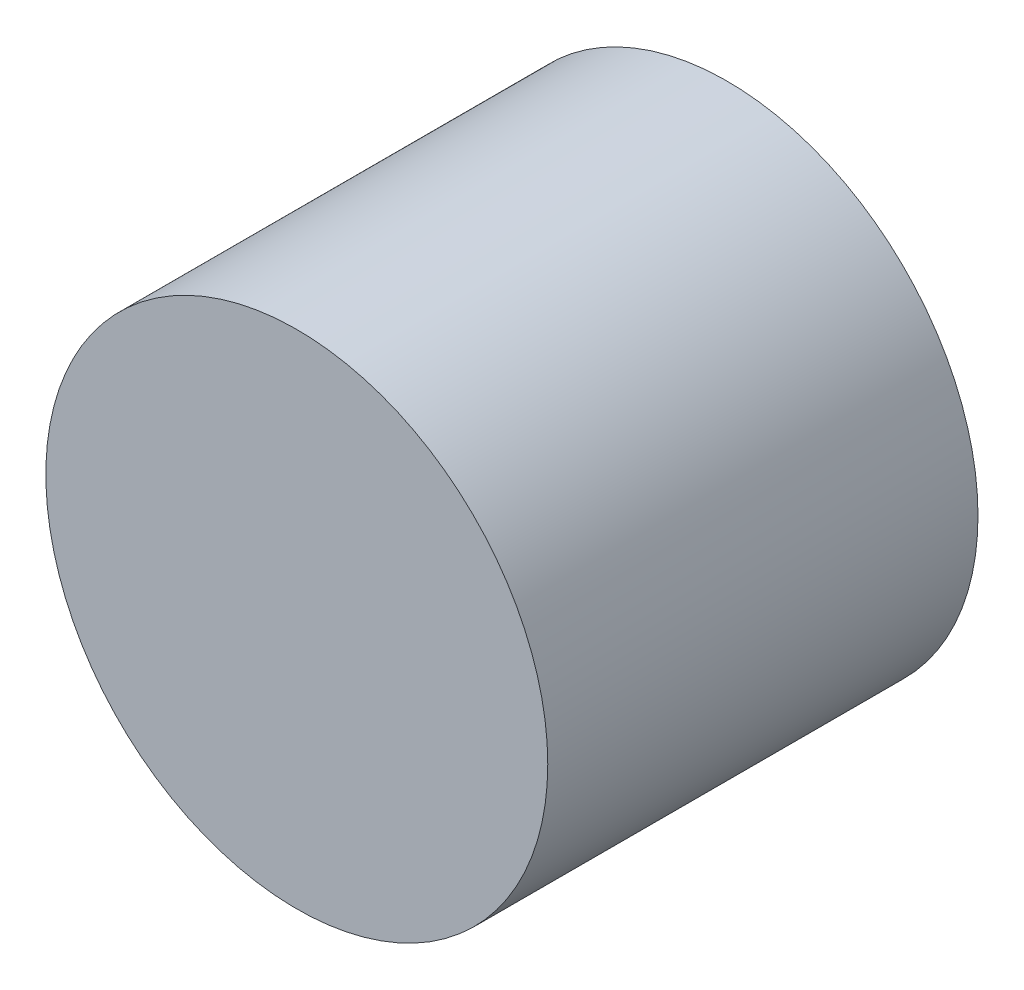
SolidWorks part; units mm, degrees
ref_plane "Front Plane" through (0, 0, 0) normal (0, 0, 1) x (1, 0, 0)
ref_plane "Top Plane" through (0, 0, 0) normal (0, 1, 0) x (1, 0, 0)
ref_plane "Right Plane" through (0, 0, 0) normal (1, 0, 0) x (0, 0, -1)
sketch "Sketch1" plane through (0, 0, 0) normal (0, 0, 1) x (1, 0, 0)
  circle A0 centre (0, 0) radius 22.225
  dimension "D1" = 44.45
extrude "Boss-Extrude1" add sketch "Sketch1" along normal blind 38.1
